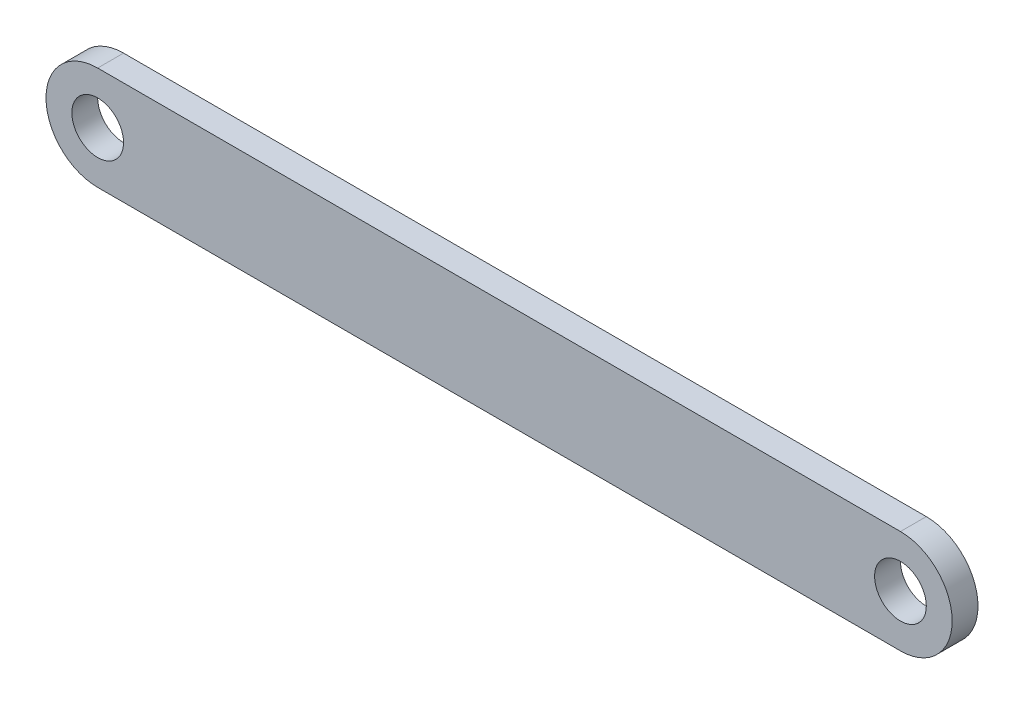
SolidWorks part; units mm, degrees
ref_plane "Front Plane" through (0, 0, 0) normal (0, 0, 1) x (1, 0, 0)
ref_plane "Top Plane" through (0, 0, 0) normal (0, 1, 0) x (1, 0, 0)
ref_plane "Right Plane" through (0, 0, 0) normal (1, 0, 0) x (0, 0, -1)
sketch "Sketch1" plane through (0, 0, 0) normal (0, 0, 1) x (1, 0, 0)
  line L1 (0, -2) -> (31.0572, -2)
  line L2 (31.0572, 2) -> (0, 2)
  arc A0 (0, 2) -> (0, -2) centre (0, 0) ccw
  arc A1 (31.0572, -2) -> (31.0572, 2) centre (31.0572, 0) ccw
  circle A2 centre (0, 0) radius 1
  circle A3 centre (31.0572, 0) radius 1
extrude "Boss-Extrude1" add sketch "Sketch1" along normal blind 1
